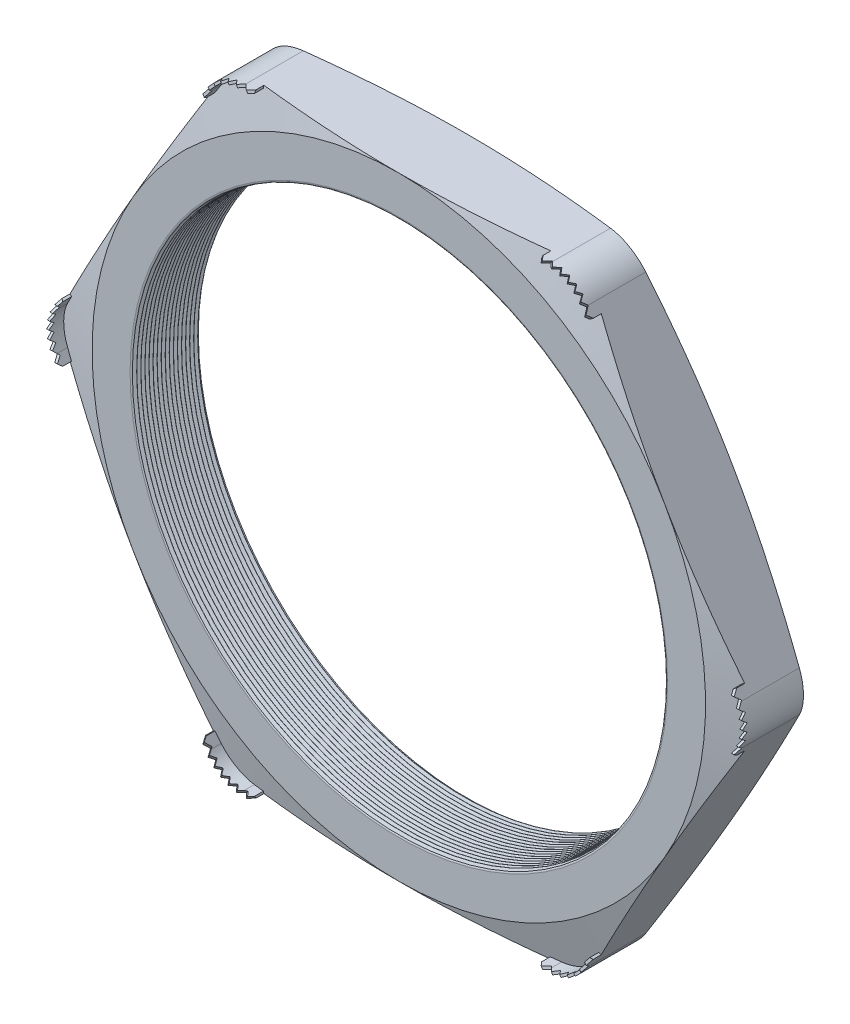
SolidWorks part; units mm, degrees
ref_plane "Front Plane" through (0, 0, 0) normal (0, 0, 1) x (1, 0, 0)
ref_plane "Top Plane" through (0, 0, 0) normal (0, 1, 0) x (1, 0, 0)
ref_plane "Right Plane" through (0, 0, 0) normal (1, 0, 0) x (0, 0, -1)
sketch "Sketch1" plane through (0, 0, 0) normal (0, 0, 1) x (1, 0, 0)
  line L1 (-26.5431, 0) -> (-13.2716, -22.987)
  line L2 (-13.2716, -22.987) -> (13.2716, -22.987)
  line L3 (13.2716, -22.987) -> (26.5431, 0)
  line L4 (26.5431, 0) -> (13.2716, 22.987)
  line L5 (13.2716, 22.987) -> (-13.2716, 22.987)
  line L6 (-13.2716, 22.987) -> (-26.5431, 0)
  circle A0 centre (0, 0) radius 22.987 construction
  circle A1 centre (0, 0) radius 19.939
  dimension "TS" = 39.878
  dimension "H" = 45.974
extrude "Extrude1" add sketch "Sketch1" along normal blind 5.08
fillet "Fillet1" radius 3.048 6 edges at (-13.2716, 22.987, 2.54) (-26.5431, 0, 2.54) (-13.2716, -22.987, 2.54) (13.2716, -22.987, 2.54) (26.5431, 0, 2.54) (13.2716, 22.987, 2.54)
sketch "Sketch2" plane through (0, 0, 5.08) normal (0, 0, 1) x (1, 0, 0)
  line L0 (-11.5118, 22.987) -> (-10.7498, 22.987)
  line L1 (11.5118, 22.987) -> (-11.5118, 22.987) construction
  line L2 (-14.1514, 21.463) -> (-14.5324, 20.8031)
  line L3 (-14.1514, 21.463) -> (-25.6632, 1.524) construction
  line L4 (-11.5118, 22.8092) -> (-10.7498, 22.8092)
  line L5 (-13.9975, 21.3741) -> (-14.3785, 20.7142)
  line L6 (-14.5324, 20.8031) -> (-14.3785, 20.7142)
  line L7 (-10.7498, 22.987) -> (-10.7498, 22.8092)
  arc A0 (-11.5118, 22.8092) -> (-13.9975, 21.3741) centre (-11.5118, 19.939) ccw
  arc A1 (-11.5118, 22.987) -> (-14.1514, 21.463) centre (-11.5118, 19.939) ccw construction
  arc A4 (-11.5118, 22.987) -> (-14.1514, 21.463) centre (-11.5118, 19.939) ccw
  dimension "D1" = 0.762
  dimension "D2" = 0.762
  dimension "OFFSET" = 0.1778
fillet "Fillet3" radius 0.2032 2 edges at (19.939, 0, 0) (19.939, 0, 5.08)
sketch "Sketch3" plane through (0, 0, 0) normal (0, 1, 0) x (1, 0, 0)
  line L0 (-19.939, -5.08) -> (-19.939, -4.7867)
  line L2 (-19.939, -4.7867) -> (-20.193, -4.9334)
  line L3 (-20.193, -4.9334) -> (-19.939, -5.08)
  line L4 (-19.939, -0.2032) -> (-19.939, -4.8768) construction
  line L5 (-14.1514, -5.08) -> (-25.6632, -5.08) construction
  dimension "D1" = 60
  dimension "D2" = 60
  dimension "D3" = 0.254
revolve "Cut-Revolve1" cut sketch "Sketch3" angle 360 about axis through (0, 0, 5.08) along (0, 0, -1)
pattern_linear "LPattern1" count 17 spacing 0.3048 along (0, 0, -1) of "Cut-Revolve1"
sketch "Sketch4" plane through (0, 0, 0) normal (0, 0, -1) x (-1, 0, 0)
  line L0 (-25.6632, 1.524) -> (-14.1514, 21.463) construction
  circle A0 centre (0, 0) radius 22.987
extrude "Cut-Extrude1" cut sketch "Sketch4" against normal through all draft 75 flip side to cut
sketch "Sketch5" plane through (0, 0, 5.08) normal (0, 0, 1) x (1, 0, 0)
  line L0 (11.5118, 22.987) -> (-11.5118, 22.987) construction
  circle A0 centre (0, 0) radius 22.987
extrude "Cut-Extrude2" cut sketch "Sketch5" against normal through all draft 75 flip side to cut
extrude "Extrude2" add sketch "Sketch2" along normal blind 0.889 and the other way up to next
ref_plane "Plane1" through (-12.5641, 21.7617, 0) normal (0.5, -0.866, 0) x (0.866, 0.5, 0)
sketch "Sketch7" plane through (-12.5641, 21.7617, 0) normal (0.5, -0.866, 0) x (0.866, 0.5, 0)
  line L0 (-2.1839, 5.0355) -> (-1.8791, 5.4089)
  line L1 (-2.1839, 4.4398) -> (-2.1839, 5.969) construction
  line L2 (0, 1.3136) -> (0, 4.0135) construction
  line L4 (-1.8791, 5.4089) -> (-1.5743, 5.0355)
  line L5 (-0.6096, 5.4089) -> (-0.3048, 5.0355)
  line L6 (-1.2192, 5.4089) -> (-0.9144, 5.0355)
  line L7 (-0.3048, 5.0355) -> (0, 5.4089)
  line L8 (0, 5.4089) -> (0.3048, 5.0355)
  line L10 (0.6096, 5.4089) -> (0.9144, 5.0355)
  line L11 (1.2192, 5.4089) -> (1.524, 5.0355)
  line L12 (-1.5743, 5.0355) -> (-1.2192, 5.4089)
  line L13 (-0.9144, 5.0355) -> (-0.6096, 5.4089)
  line L14 (0.3048, 5.0355) -> (0.6096, 5.4089)
  line L15 (1.8791, 5.4089) -> (2.1839, 5.0355)
  line L16 (2.1839, 4.4398) -> (2.1839, 5.969) construction
  line L17 (-2.1839, 5.0355) -> (-2.1839, 5.969)
  line L19 (-2.1839, 5.969) -> (2.1839, 5.969)
  line L20 (2.1839, 5.969) -> (2.1839, 5.0355)
  line L23 (0.9144, 5.0355) -> (1.2192, 5.4089)
  line L25 (1.524, 5.0355) -> (1.8791, 5.4089)
  dimension "D1" = 0.9335
  dimension "D2" = 0.5601
  dimension "D3" = 0.3048
extrude "Cut-Extrude4" cut sketch "Sketch7" against normal through all
pattern_circular "CirPattern1" count 6 over 360 about axis through (0, 0, 0) along (0, 0, 1) of "Extrude2"
pattern_circular "CirPattern2" count 6 over 360 about axis through (0, 0, 0) along (0, 0, 1) of "Cut-Extrude4"
